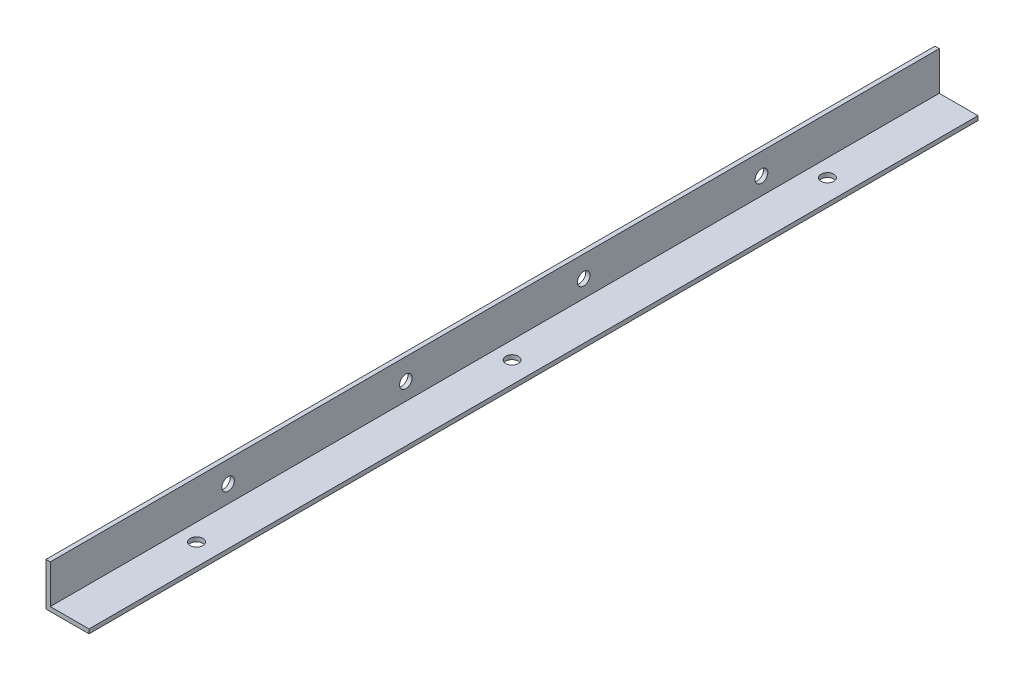
SolidWorks part; units mm, degrees
ref_plane "正面" through (0, 0, 0) normal (0, 0, 1) x (1, 0, 0)
ref_plane "平面" through (0, 0, 0) normal (0, 1, 0) x (1, 0, 0)
ref_plane "右側面" through (0, 0, 0) normal (1, 0, 0) x (0, 0, -1)
sketch "ｽｹｯﾁ1" plane through (0, 0, 0) normal (0, 0, 1) x (1, 0, 0)
  line L0 (0, 0) -> (0, -15)
  line L1 (0, -15) -> (15, -15)
  line L2 (15, -15) -> (15, -13.5)
  line L3 (15, -13.5) -> (1.5, -13.5)
  line L4 (1.5, -13.5) -> (1.5, 0)
  line L5 (1.5, 0) -> (0, 0)
  dimension "D1" = 1.5
  dimension "D2" = 1.5
  dimension "D3" = 15
  dimension "D4" = 15
extrude "ﾎﾞｽ - 押し出し1" add sketch "ｽｹｯﾁ1" along normal blind 310
sketch "ｽｹｯﾁ2" plane through (0, 0, 0) normal (-1, 0, 0) x (0, 0, 1)
  line L0 (310, -7.5) -> (248, -7.5)
  line L1 (310, 0) -> (310, -15) construction
  line L2 (248, -7.5) -> (186, -7.5)
  line L3 (0, -7.5) -> (62, -7.5)
  line L4 (0, 0) -> (0, -15) construction
  line L5 (62, -7.5) -> (124, -7.5)
  circle A0 centre (248, -7.5) radius 2.2
  circle A1 centre (186, -7.5) radius 2.2
  circle A2 centre (124, -7.5) radius 2.2
  circle A3 centre (62, -7.5) radius 2.2
  dimension "D5" = 4.4
  dimension "D6" = 4.4
  dimension "D7" = 4.4
  dimension "D8" = 4.4
  dimension "D1" = 62
  dimension "D2" = 62
  dimension "D3" = 62
  dimension "D4" = 62
extrude "ｶｯﾄ - 押し出し1" cut sketch "ｽｹｯﾁ2" against normal blind 310
sketch "ｽｹｯﾁ3" plane through (0, -15, 0) normal (0, -1, 0) x (-1, 0, 0)
  line L0 (-15, -155) -> (-7.5, -155)
  line L1 (-15, -310) -> (-15, 0) construction
  line L2 (-7.5, -155) -> (-7.5, -45)
  line L3 (-7.5, -155) -> (-7.5, -265)
  circle A0 centre (-7.5, -265) radius 2.2
  circle A1 centre (-7.5, -155) radius 2.2
  circle A2 centre (-7.5, -45) radius 2.2
  dimension "D4" = 4.4
  dimension "D5" = 4.4
  dimension "D6" = 4.4
  dimension "D1" = 110
  dimension "D2" = 110
  dimension "D3" = 7.5
extrude "ｶｯﾄ - 押し出し2" cut sketch "ｽｹｯﾁ3" against normal blind 160
